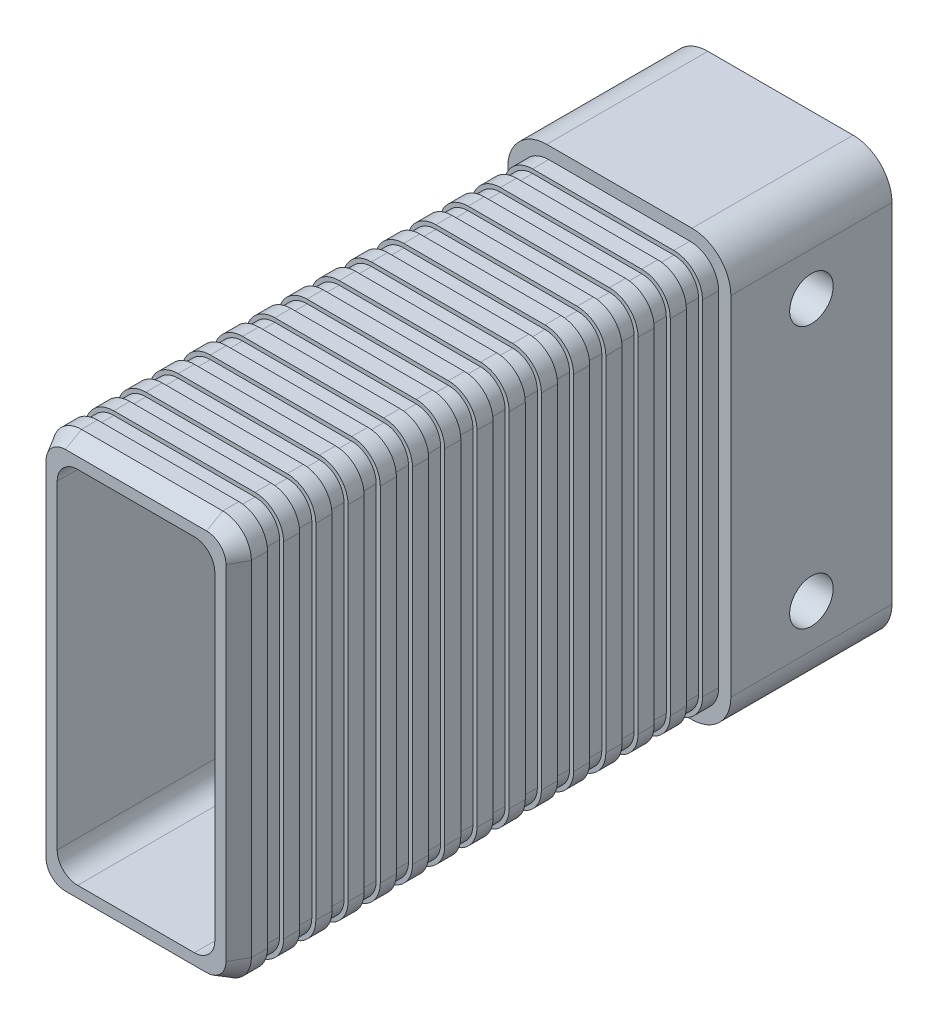
SolidWorks part; units mm, degrees
material "Nylon 101"
ref_plane "Front Plane" through (0, 0, 0) normal (0, 0, 1) x (1, 0, 0)
ref_plane "Top Plane" through (0, 0, 0) normal (0, 1, 0) x (1, 0, 0)
ref_plane "Right Plane" through (0, 0, 0) normal (1, 0, 0) x (0, 0, -1)
sketch "Sketch1" plane through (0, 0, 0) normal (0, 0, 1) x (1, 0, 0)
  line L1 (12.323, -24.896) -> (-12.323, -24.896)
  line L2 (12.323, -24.896) -> (12.323, 24.896)
  line L3 (12.323, 24.896) -> (-12.323, 24.896)
  line L4 (-12.323, -24.896) -> (-12.323, 24.896)
  line L5 (12.323, -24.896) -> (-12.323, 24.896) construction
  line L6 (12.323, 24.896) -> (-12.323, -24.896) construction
  point P0 (0, 0)
  dimension "D1" = 49.792
  dimension "D2" = 24.646
extrude "Boss-Extrude1" add sketch "Sketch1" along normal blind 60
sketch "Sketch2" plane through (0, 0, 0) normal (0, 0, 1) x (1, 0, 0)
  line L1 (13.843, -26.416) -> (-13.843, -26.416)
  line L2 (13.843, -26.416) -> (13.843, 26.416)
  line L3 (13.843, 26.416) -> (-13.843, 26.416)
  line L4 (-13.843, -26.416) -> (-13.843, 26.416)
  line L5 (13.843, -26.416) -> (-13.843, 26.416) construction
  line L6 (13.843, 26.416) -> (-13.843, -26.416) construction
  point P0 (0, 0)
  dimension "D1" = 52.832
  dimension "D2" = 27.686
extrude "Boss-Extrude2" add sketch "Sketch2" against normal blind 20
fillet "Fillet1" radius 3.556 4 edges at (-12.323, -24.896, 30) (12.323, -24.896, 30) (12.323, 24.896, 30) (-12.323, 24.896, 30)
fillet "Fillet2" radius 4.826 4 edges at (-13.843, 26.416, -10) (13.843, 26.416, -10) (13.843, -26.416, -10) (-13.843, -26.416, -10)
sketch "Sketch4" plane through (13.843, 0, 0) normal (1, 0, 0) x (0, 0, -1)
  line L0 (10, 26.416) -> (10, 16.256) construction
  line L1 (0, 26.416) -> (20, 26.416) construction
  line L2 (0, 18.0158) -> (10, 18.0158) construction
  line L4 (0, -21.34) -> (0, 21.34) construction
  line L5 (10, 16.0542) -> (20, 16.0542) construction
  line L6 (20, -21.59) -> (20, 21.59) construction
  line L7 (5.9262, 0) -> (-5.9262, 0) construction
  point P11 (10, 16.256)
  point P18 (10, -16.256)
  dimension "D1" = 10.16
hole_wizard "Ø5.0mm Dowel Hole2" positions "Sketch7" profile "Sketch8" hole size "Ø5.0" standard "ANSI Metric" end condition through all
sketch "Sketch7" plane through (13.843, 0, 0) normal (1, 0, 0) x (0, 0, -1)
  point P0 (10, 16.256)
  point P3 (10, -16.256)
sketch "Sketch8" plane through (13.843, 16.256, -10) normal (0, 1, 0) x (0, 0, -1)
  line L0 (0, 0) -> (0, 27.686)
  line L1 (0, 27.686) -> (2.7, 27.686)
  line L2 (2.7, 27.686) -> (2.7, 0)
  line L5 (2.7, 0) -> (0, 0)
  line L11 (0, -6.35) -> (0, 107.95) construction
  dimension "Thru Hole Dia." = 5.4
  dimension "Thru Hole Depth" = 27.686
sketch "Sketch9" plane through (0, 0, 60) normal (0, 0, 1) x (1, 0, 0)
  line L0 (8.767, 24.896) -> (-8.767, 24.896) construction
  line L1 (7.243, -22.356) -> (-7.243, -22.356)
  line L2 (9.783, -19.816) -> (9.783, 19.816)
  line L3 (7.243, 22.356) -> (-7.243, 22.356)
  line L4 (-9.783, -19.816) -> (-9.783, 19.816)
  line L5 (9.783, -22.356) -> (-9.783, 22.356) construction
  line L6 (9.783, 22.356) -> (-9.783, -22.356) construction
  line L7 (12.323, -21.34) -> (12.323, 21.34) construction
  arc A0 (7.243, -22.356) -> (9.783, -19.816) centre (7.243, -19.816) ccw
  arc A1 (-7.243, -22.356) -> (-9.783, -19.816) centre (-7.243, -19.816) cw
  arc A2 (-7.243, 22.356) -> (-9.783, 19.816) centre (-7.243, 19.816) ccw
  arc A3 (9.783, 19.816) -> (7.243, 22.356) centre (7.243, 19.816) ccw
  point P0 (0, 0)
  dimension "D3" = 2.54
  dimension "D1" = 2.54
  dimension "D2" = 2.54
extrude "Cut-Extrude1" cut sketch "Sketch9" against normal through all
sketch "Sketch10" plane through (0, 0, 60) normal (0, 0, 1) x (1, 0, 0)
  line L9 (-12.323, 21.34) -> (-12.323, -21.34)
  line L10 (-8.767, -24.896) -> (8.767, -24.896)
  line L11 (12.323, -21.34) -> (12.323, 21.34)
  line L12 (8.767, 24.896) -> (-8.767, 24.896)
  line L13 (-11.823, 21.34) -> (-11.823, -21.34)
  line L14 (-8.767, -24.396) -> (8.767, -24.396)
  line L15 (11.823, -21.34) -> (11.823, 21.34)
  line L16 (8.767, 24.396) -> (-8.767, 24.396)
  line L17 (-11.823, 21.34) -> (-11.823, -21.34)
  line L18 (-8.767, -24.396) -> (8.767, -24.396)
  line L19 (11.823, -21.34) -> (11.823, 21.34)
  line L20 (8.767, 24.396) -> (-8.767, 24.396)
  arc A8 (-8.767, 24.896) -> (-12.323, 21.34) centre (-8.767, 21.34) ccw
  arc A9 (-12.323, -21.34) -> (-8.767, -24.896) centre (-8.767, -21.34) ccw
  arc A10 (8.767, -24.896) -> (12.323, -21.34) centre (8.767, -21.34) ccw
  arc A11 (12.323, 21.34) -> (8.767, 24.896) centre (8.767, 21.34) ccw
  arc A12 (-11.823, -21.34) -> (-8.767, -24.396) centre (-8.767, -21.34) ccw
  arc A13 (8.767, -24.396) -> (11.823, -21.34) centre (8.767, -21.34) ccw
  arc A14 (11.823, 21.34) -> (8.767, 24.396) centre (8.767, 21.34) ccw
  arc A15 (-8.767, 24.396) -> (-11.823, 21.34) centre (-8.767, 21.34) ccw
  arc A16 (-11.823, -21.34) -> (-8.767, -24.396) centre (-8.767, -21.34) ccw
  arc A17 (8.767, -24.396) -> (11.823, -21.34) centre (8.767, -21.34) ccw
  arc A18 (11.823, 21.34) -> (8.767, 24.396) centre (8.767, 21.34) ccw
  arc A19 (-8.767, 24.396) -> (-11.823, 21.34) centre (-8.767, 21.34) ccw
  dimension "D1" = 0.5
extrude "Cut-Extrude2" cut sketch "Sketch10" against normal blind 2 from offset 4 offset against normal yes
pattern_linear "LPattern1" count 14 spacing 4 along (0, 0, -1) of "Cut-Extrude2"
chamfer "Chamfer1" distance 2 angle 30 8 edges at (12.323, 0, 60) (11.2815, 23.8545, 60) (11.2815, -23.8545, 60) (0, 24.896, 60) (0, -24.896, 60) (-11.2815, 23.8545, 60) (-11.2815, -23.8545, 60) (-12.323, 0, 60)
